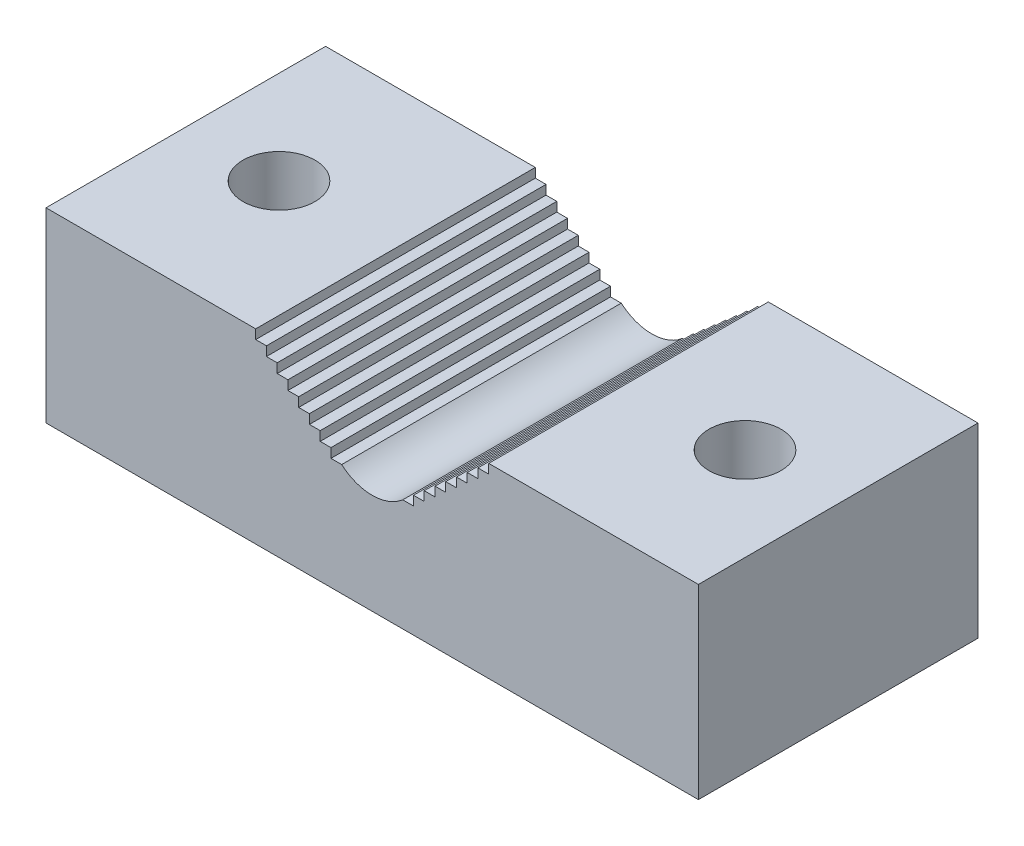
SolidWorks part; units mm, degrees
material "6061-T6 (SS)"
ref_plane "Front Plane" through (0, 0, 0) normal (0, 0, 1) x (1, 0, 0)
ref_plane "Top Plane" through (0, 0, 0) normal (0, 1, 0) x (1, 0, 0)
ref_plane "Right Plane" through (0, 0, 0) normal (1, 0, 0) x (0, 0, -1)
sketch "Sketch1" plane through (0, 0, 0) normal (0, 0, 1) x (1, 0, 0)
  line L0 (-44.45, 0) -> (44.45, 0)
  line L1 (44.45, 0) -> (44.45, 25.4)
  line L2 (44.45, 25.4) -> (-44.45, 25.4)
  line L3 (-44.45, 25.4) -> (-44.45, 0)
  point P3 (0, 0)
  dimension "D1" = 25.4
  dimension "D2" = 88.9
extrude "Boss-Extrude1" add sketch "Sketch1" against normal blind 38.1
sketch "Sketch2" plane through (0, 0, 0) normal (0, 0, 1) x (1, 0, 0)
  line L0 (-15.875, 25.4) -> (-4.1606, 15.24) construction
  line L1 (-15.875, 25.4) -> (0, 25.4)
  line L2 (44.45, 25.4) -> (-44.45, 25.4) construction
  line L3 (15.875, 25.4) -> (4.1606, 15.24) construction
  line L4 (15.875, 25.4) -> (0, 25.4)
  line L5 (-15.875, 25.4) -> (-15.875, 24.13)
  line L6 (-15.875, 24.13) -> (-14.4107, 24.13)
  line L7 (-14.4107, 24.13) -> (-14.4107, 22.86)
  line L8 (-14.4107, 22.86) -> (-12.9464, 22.86)
  line L9 (-12.9464, 22.86) -> (-12.9464, 21.59)
  line L10 (-12.9464, 21.59) -> (-11.4821, 21.59)
  line L11 (-11.4821, 21.59) -> (-11.4821, 20.32)
  line L12 (-11.4821, 20.32) -> (-10.0178, 20.32)
  line L13 (-10.0178, 20.32) -> (-10.0178, 19.05)
  line L14 (-10.0178, 19.05) -> (-8.5535, 19.05)
  line L15 (-8.5535, 19.05) -> (-8.5535, 17.78)
  line L16 (-8.5535, 17.78) -> (-7.0892, 17.78)
  line L17 (-7.0892, 17.78) -> (-7.0892, 16.51)
  line L18 (-7.0892, 16.51) -> (-5.6249, 16.51)
  line L19 (-5.6249, 16.51) -> (-5.6249, 15.24)
  line L20 (-5.6249, 15.24) -> (-4.1606, 15.24)
  line L21 (0, 25.4) -> (0, 0) construction
  line L24 (5.6249, 15.24) -> (4.1606, 15.24)
  line L25 (5.6249, 16.51) -> (5.6249, 15.24)
  line L26 (7.0892, 16.51) -> (5.6249, 16.51)
  line L27 (7.0892, 17.78) -> (7.0892, 16.51)
  line L28 (8.5535, 17.78) -> (7.0892, 17.78)
  line L29 (8.5535, 19.05) -> (8.5535, 17.78)
  line L30 (10.0178, 19.05) -> (8.5535, 19.05)
  line L31 (10.0178, 20.32) -> (10.0178, 19.05)
  line L32 (11.4821, 20.32) -> (10.0178, 20.32)
  line L33 (11.4821, 21.59) -> (11.4821, 20.32)
  line L34 (12.9464, 21.59) -> (11.4821, 21.59)
  line L35 (12.9464, 22.86) -> (12.9464, 21.59)
  line L36 (14.4107, 22.86) -> (12.9464, 22.86)
  line L37 (14.4107, 24.13) -> (14.4107, 22.86)
  line L38 (15.875, 24.13) -> (14.4107, 24.13)
  line L39 (15.875, 25.4) -> (15.875, 24.13)
  arc A0 (4.1606, 15.24) -> (-4.1606, 15.24) centre (0, 20.0371) cw
  point P7 (0, 25.4)
  dimension "D1" = 6.35
  dimension "D2" = 31.75
  dimension "D4" = 1.27
extrude "Cut-Extrude1" cut sketch "Sketch2" against normal up to next
sketch "Sketch3" plane through (0, 0, 0) normal (0, 0, 1) x (1, 0, 0)
  circle A0 centre (0, 24.151) radius 14.2875
  dimension "D1" = 28.575
hole_wizard "3/8 Clearance Hole1" positions "Sketch6" profile "Sketch5" hole size "3/8" standard "ANSI Inch" end condition through all
sketch "Sketch6" plane through (0, 25.4, 0) normal (0, 1, 0) x (1, 0, 0)
  line L1 (-44.45, 38.1) -> (-44.45, 0) construction
  line L3 (44.45, 38.1) -> (44.45, 0) construction
  point P0 (-31.75, 19.05)
  point P2 (31.75, 19.05)
  point P10 (-44.45, 19.05)
  point P16 (44.45, 19.05)
  dimension "D1" = 12.7
  dimension "D2" = 12.7
sketch "Sketch5" plane through (-31.75, 25.4, -19.05) normal (1, 0, 0) x (0, 0, 1)
  line L0 (0, 0) -> (0, 25.4)
  line L1 (0, 25.4) -> (4.9022, 25.4)
  line L2 (4.9022, 25.4) -> (4.9022, 0)
  line L5 (4.9022, 0) -> (0, 0)
  line L11 (0, -6.35) -> (0, 107.95) construction
  dimension "Thru Hole Dia." = 9.8044
  dimension "Thru Hole Depth" = 25.4
